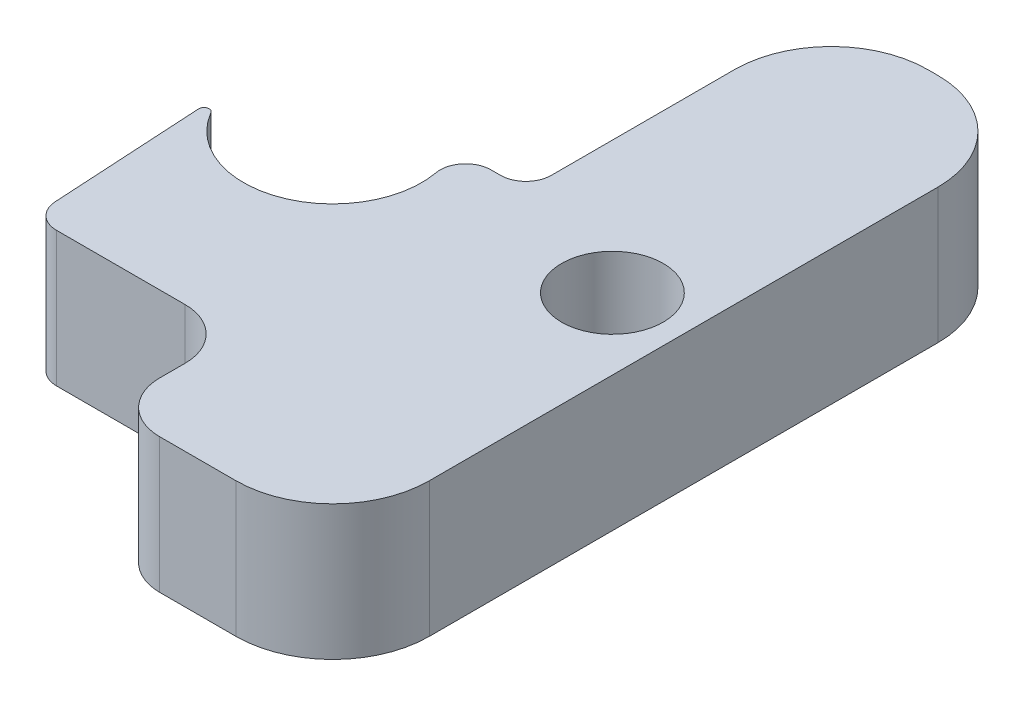
SolidWorks part; units mm, degrees
ref_plane "Front Plane" through (0, 0, 0) normal (0, 0, 1) x (1, 0, 0)
ref_plane "Top Plane" through (0, 0, 0) normal (0, 1, 0) x (1, 0, 0)
ref_plane "Right Plane" through (0, 0, 0) normal (1, 0, 0) x (0, 0, -1)
sketch "Sketch1" plane through (0, 0, 0) normal (0, 1, 0) x (1, 0, 0)
  line L0 (2.9, 5) -> (2.9, 1.4)
  line L1 (4.8, 6.9) -> (5, 6.9)
  line L2 (-6.9, 0.65) -> (-6.9, -5)
  line L3 (-5, -6.9) -> (-3.5, -6.9)
  line L4 (6.9, 5) -> (6.9, -5)
  line L5 (-6.9, 6.9) -> (6.9, -6.9) construction
  line L6 (-6.9, -6.9) -> (6.9, 6.9) construction
  line L7 (2.4, 0.9) -> (2.2142, 0.9)
  line L8 (-2.2142, 0.9) -> (-4.0543, 0.9)
  line L9 (0, 3.7493) -> (0, -4.6595) construction
  line L10 (-6.5677, 0.9) -> (-6.65, 0.9)
  line L11 (3.5, -6.9) -> (5, -6.9)
  line L12 (-1.5, -4.4) -> (1.5, -4.4)
  line L13 (-2.5, -5.4) -> (-2.5, -5.9)
  line L15 (2.5, -5.4) -> (2.5, -5.9)
  line L16 (-2.5, -4.4) -> (2.5, -6.9) construction
  line L17 (-2.5, -6.9) -> (2.5, -4.4) construction
  line L18 (-1.5271, -3.9287) -> (-1.7471, -0.1004)
  line L19 (-1.5, -4.4) -> (-1.5271, -3.9287) construction
  arc A0 (-1.7221, 0.3111) -> (1.7221, 0.3111) centre (0, 0) ccw
  arc A1 (-6.3542, 0.52) -> (-4.5362, 0.2667) centre (-5.5, 0) ccw
  circle A2 centre (5.5, 0) radius 1
  arc A3 (2.9, 5) -> (4.8, 6.9) centre (4.8, 5) cw
  arc A4 (5, 6.9) -> (6.9, 5) centre (5, 5) cw
  arc A5 (-6.9, -5) -> (-5, -6.9) centre (-5, -5) ccw
  arc A6 (5, -6.9) -> (6.9, -5) centre (5, -5) ccw
  arc A7 (2.9, 1.4) -> (2.4, 0.9) centre (2.4, 1.4) cw
  arc A8 (1.7221, 0.3111) -> (2.2142, 0.9) centre (2.2142, 0.4) cw
  arc A9 (-1.7221, 0.3111) -> (-2.2142, 0.9) centre (-2.2142, 0.4) ccw
  arc A10 (-4.0543, 0.9) -> (-4.5362, 0.2667) centre (-4.0543, 0.4) ccw
  arc A11 (-6.65, 0.9) -> (-6.9, 0.65) centre (-6.65, 0.65) ccw
  arc A12 (-6.5677, 0.9) -> (-6.3542, 0.52) centre (-6.5677, 0.65) cw
  arc A13 (1.5, -4.4) -> (2.5, -5.4) centre (1.5, -5.4) cw
  arc A14 (-1.5, -4.4) -> (-2.5, -5.4) centre (-1.5, -5.4) ccw
  arc A15 (3.5, -6.9) -> (2.5, -5.9) centre (3.5, -5.9) cw
  arc A16 (-2.5, -5.9) -> (-3.5, -6.9) centre (-3.5, -5.9) cw
  arc A17 (-1.0279, -4.4) -> (-1.5271, -3.9287) centre (-1.0279, -3.9) cw
  arc A18 (-1.5128, -0.8797) -> (-1.6991, -0.9357) centre (-1.5993, -0.93) ccw
  point P0 (0, 0)
  point P10 (0, -5.65)
  point P22 (2.9, 6.9)
  point P34 (2.9, 0.9)
  point P43 (-6.9, 0.9)
  point P69 (0, 0)
  point P70 (0, 0)
  point P71 (0, 0)
  point P72 (-1.4703, -0.9491)
  point P73 (-1.6926, -1.0484)
  point P74 (0, 0)
  dimension "D4" = 3.5
  dimension "D6" = 2
  dimension "D7" = 2
  dimension "D9" = 1.9
  dimension "D10" = 0.5
  dimension "D11" = 0.25
  dimension "D14" = 1
  dimension "D15" = 0.5
  dimension "D16" = 0.1
  dimension "D1" = 13.8
  dimension "D2" = 6
  dimension "D3" = 9.8
  dimension "D5" = 13.8
  dimension "D8" = 11
  dimension "D12" = 2.5
  dimension "D13" = 5
extrude "Boss-Extrude1" add sketch "Sketch1" along normal blind 2.65 contours A17 L12 A13 L15 A15 L11 A6 L4 A4 L1 A3 L0 A7 L7 A8 A0 L18 A2
